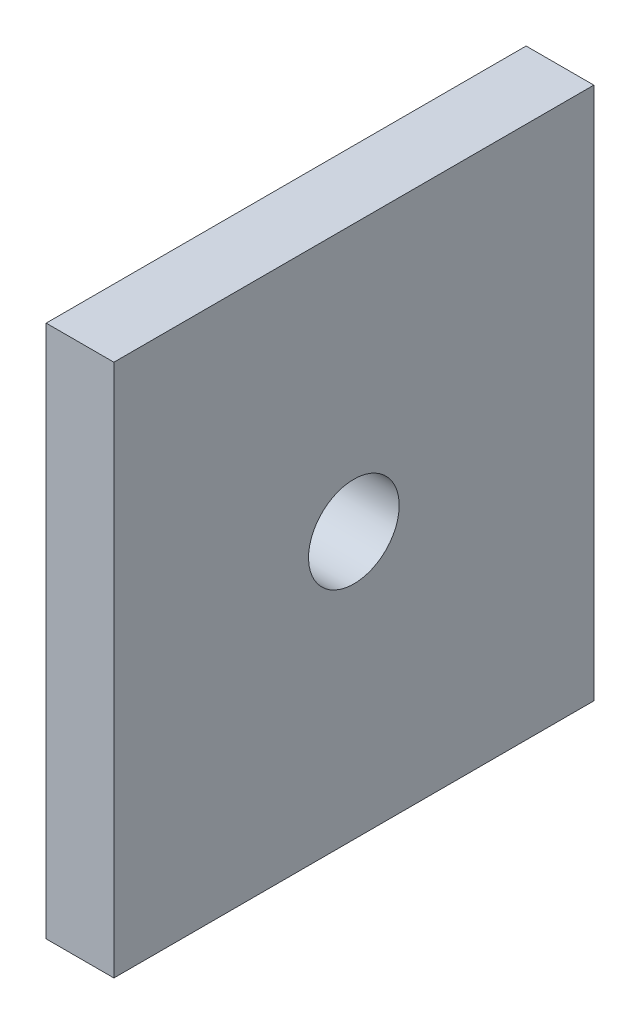
SolidWorks part; units mm, degrees
ref_plane "Front Plane" through (0, 0, 0) normal (0, 0, 1) x (1, 0, 0)
ref_plane "Top Plane" through (0, 0, 0) normal (0, 1, 0) x (1, 0, 0)
ref_plane "Right Plane" through (0, 0, 0) normal (1, 0, 0) x (0, 0, -1)
sketch "Sketch3" plane through (0, 0, 0) normal (0, 0, 1) x (1, 0, 0)
  line L1 (0, 0) -> (6.35, 0)
  line L2 (0, 0) -> (0, 50)
  line L3 (0, 50) -> (6.35, 50)
  line L4 (6.35, 0) -> (6.35, 50)
  dimension "D1" = 50
  dimension "D2" = 6.35
extrude "Boss-Extrude2" add sketch "Sketch3" along normal blind 45
sketch "Sketch4" plane through (6.35, 0, 0) normal (1, 0, 0) x (0, 0, -1)
  line L0 (-45, 0) -> (-45, 50) construction
  line L1 (-45, 0) -> (0, 0) construction
  circle A0 centre (-22.5, 25) radius 4.25
  dimension "D2" = 25
  dimension "D3" = 8.5
  dimension "D1" = 22.5
extrude "Cut-Extrude1" cut sketch "Sketch4" against normal through all contours A0
